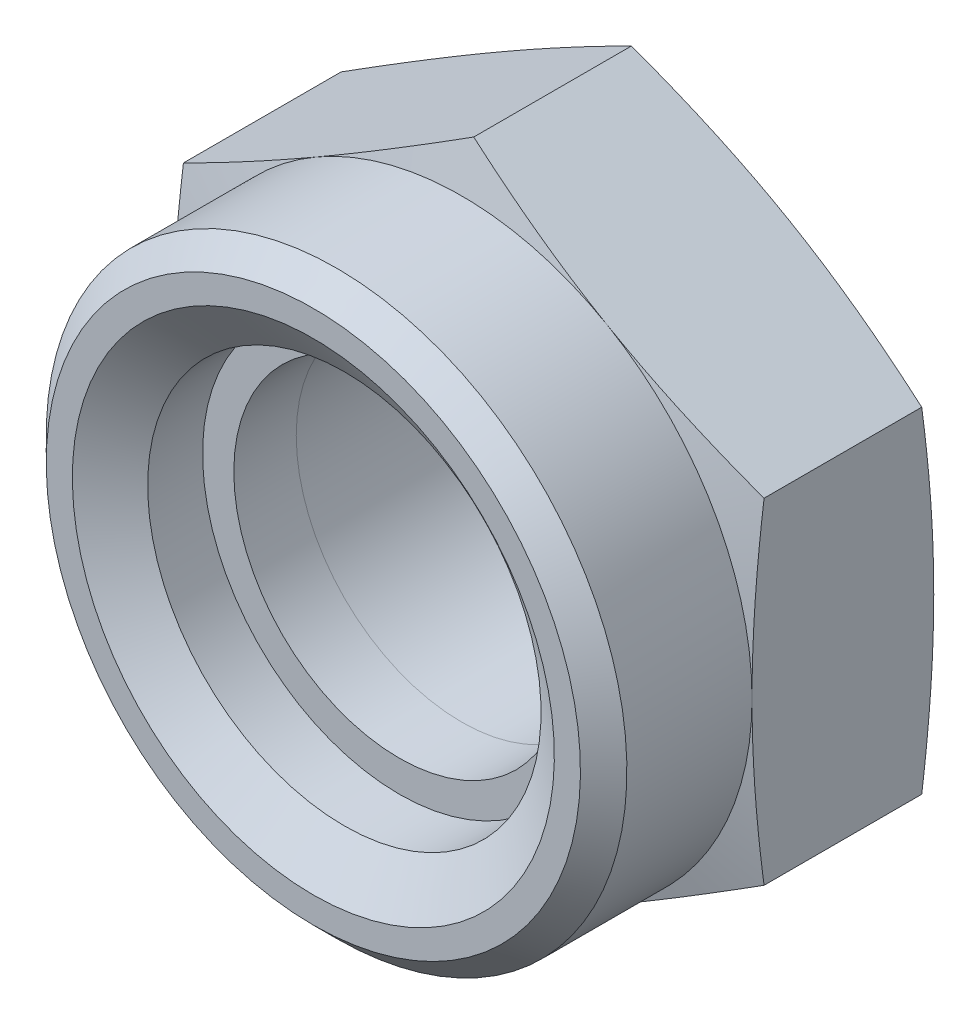
SolidWorks part; units mm, degrees
extrude "基体-拉伸" add sketch "草图1" along normal blind 5.7
sketch "草图1" plane through (0, 0, 0) normal (0, 0, 1) x (1, 0, 0)
  line L0 (0, 69.3454) -> (0, -55.7623) construction
  line L2 (0, 10.2364) -> (-8.865, 5.1182)
  line L3 (-8.865, 5.1182) -> (-8.865, -5.1182)
  line L4 (-8.865, -5.1182) -> (0, -10.2364)
  line L5 (0, -10.2364) -> (8.865, -5.1182)
  line L6 (8.865, -5.1182) -> (8.865, 5.1182)
  line L7 (8.865, 5.1182) -> (0, 10.2364)
  circle A0 centre (0, 0) radius 8.865 construction
  circle A1 centre (0, 0) radius 5.0528
  dimension "D2" = 17.73
  dimension "D1" = 10.1056
cosmetic thread "装饰螺纹线1"
ref_plane "基准面1" through (0, 0, 0) normal (0, 0, 1) x (1, 0, 0)
ref_plane "基准面2" through (0, 0, 0) normal (0, 1, 0) x (1, 0, 0)
ref_plane "基准面3" through (0, 0, 0) normal (1, 0, 0) x (0, 0, -1)
sketch "尺寸草图" plane through (0, 0, 0) normal (0, 0, 1) x (1, 0, 0)
  line L0 (0, 0) -> (4.56, 0) construction
  line L1 (0, 0) -> (1.75, 0) construction
  line L2 (-9.6244, 0) -> (0, 0) construction
  point P3 (12, 0)
  point P4 (12, 0)
  point P5 (16.6, 0)
  point P6 (10.23, 0)
  point P7 (5.7, 0)
  point P8 (20.03, 0)
  point P9 (4.56, 0)
  point P11 (17.73, 0)
  dimension "D1" = 9.6244
  dimension "D" = 12
  dimension "da" = 12
  dimension "dw" = 16.6
  dimension "h" = 10.23
  dimension "m" = 5.7
  dimension "e" = 20.03
  dimension "mw" = 4.56
  dimension "s" = 17.73
  dimension "P" = 1.75
sketch "草图8" plane through (0, 0, 0) normal (0, 0, -1) x (-1, 0, 0)
  circle A0 centre (0, 0) radius 8.3
  dimension "s" = 16.6
extrude "切除-拉伸4" cut sketch "草图8" against normal through all draft 75 flip side to cut
sketch "草图11" plane through (0, 0, 5.7) normal (0, 0, 1) x (1, 0, 0)
  circle A0 centre (0, 0) radius 8.865
  circle A1 centre (0, 0) radius 17.73
  dimension "D1" = 17.73
  dimension "D2" = 35.46
extrude "切除-拉伸5" cut sketch "草图11" against normal blind 1 draft 75
sketch "草图9" plane through (0, 0, 0) normal (1, 0, 0) x (0, 0, -1)
  line L0 (-5.7, 8.865) -> (-10.23, 8.865)
  line L1 (-5.7, 6.9589) -> (-5.7, 5.0528) construction
  line L2 (-10.23, 8.865) -> (-10.23, 6.0059)
  line L3 (0, 0) -> (-10.23, 0) construction
  line L4 (-5.7, 8.865) -> (-5.7, 6.9589)
  line L5 (-5.7, 5.0528) -> (-5.7, -5.0528) construction
  line L6 (-5.7, 6.9589) -> (-7.6061, 6.9589)
  line L7 (-7.6061, 6.9589) -> (-7.6061, 6.0059)
  line L8 (-7.6061, 6.0059) -> (-10.23, 6.0059)
  line L9 (-7.6061, 6.0059) -> (-7.6061, 5.0528) construction
  line L10 (-7.6061, 5.0528) -> (-5.7, 5.0528) construction
  line L11 (-5.7, 5.1182) -> (-5.7, 10.2364) construction
  line L12 (-5.7, -5.1182) -> (-5.7, 5.1182) construction
  dimension "D1" = 10.23
  dimension "D2" = 17.73
  dimension "D3" = 13.9178
  dimension "D5" = 10.1056
revolve "旋转1" add sketch "草图9" angle 360 mid plane about L3
sketch "草图10" plane through (0, 0, 0) normal (1, 0, 0) x (0, 0, -1)
  line L0 (-7.6061, 5.0528) -> (-7.6061, 6.9589)
  line L1 (-7.6061, 6.9589) -> (-5.7, 6.9589)
  line L2 (-5.7, 6.9589) -> (-5.7, 5.0528)
  line L3 (-5.7, 5.0528) -> (-7.6061, 5.0528)
  line L4 (0, 0) -> (-10.23, 0) construction
  line L5 (0, 0) -> (-10.23, 0) construction
revolve "旋转2" add sketch "草图10" angle 360 mid plane about L5
chamfer "倒角1" distance 0.7092 angle 45 1 edges at (0, 8.865, 10.23)
chamfer "倒角2" distance 0.9472 angle 55 2 edges at (0, 6.0059, 10.23) (5.0528, 0, 0)
